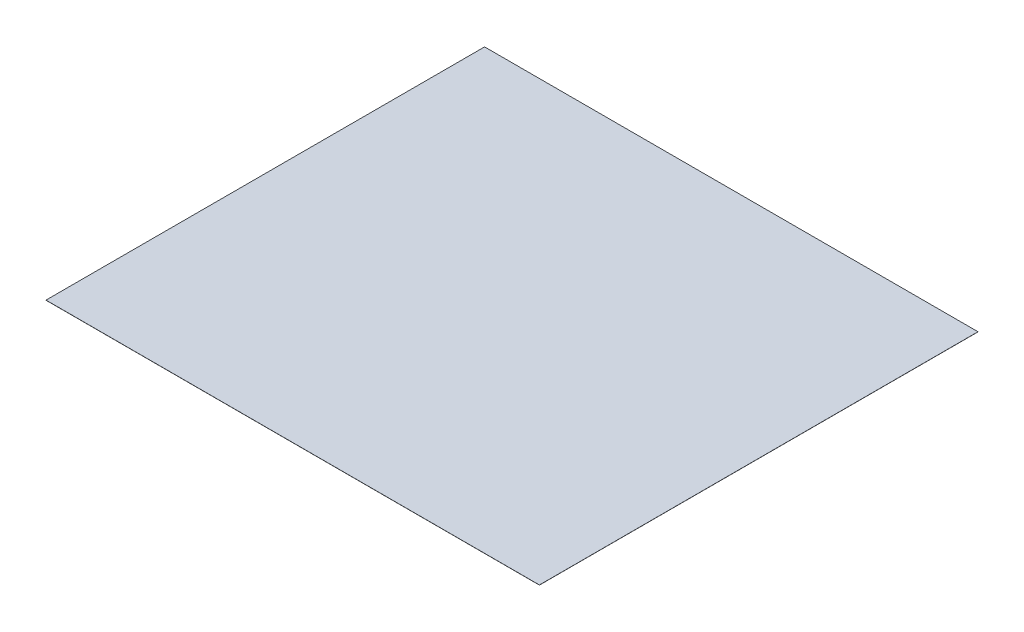
SolidWorks part; units mm, degrees
material "PE High Density Film"
ref_plane "Front Plane" through (0, 0, 0) normal (0, 0, 1) x (1, 0, 0)
ref_plane "Top Plane" through (0, 0, 0) normal (0, 1, 0) x (1, 0, 0)
ref_plane "Right Plane" through (0, 0, 0) normal (1, 0, 0) x (0, 0, -1)
sketch "Sketch1" plane through (0, 0, 0) normal (0, 1, 0) x (1, 0, 0)
  line L1 (-2743.2, -2438.4) -> (2743.2, -2438.4)
  line L2 (-2743.2, -2438.4) -> (-2743.2, 2438.4)
  line L3 (-2743.2, 2438.4) -> (2743.2, 2438.4)
  line L4 (2743.2, -2438.4) -> (2743.2, 2438.4)
  line L5 (-2743.2, -2438.4) -> (2743.2, 2438.4) construction
  line L6 (-2743.2, 2438.4) -> (2743.2, -2438.4) construction
  point P0 (0, 0)
  dimension "D1" = 4876.8
  dimension "D2" = 5486.4
extrude "Boss-Extrude1" add sketch "Sketch1" along normal blind 1.5875
